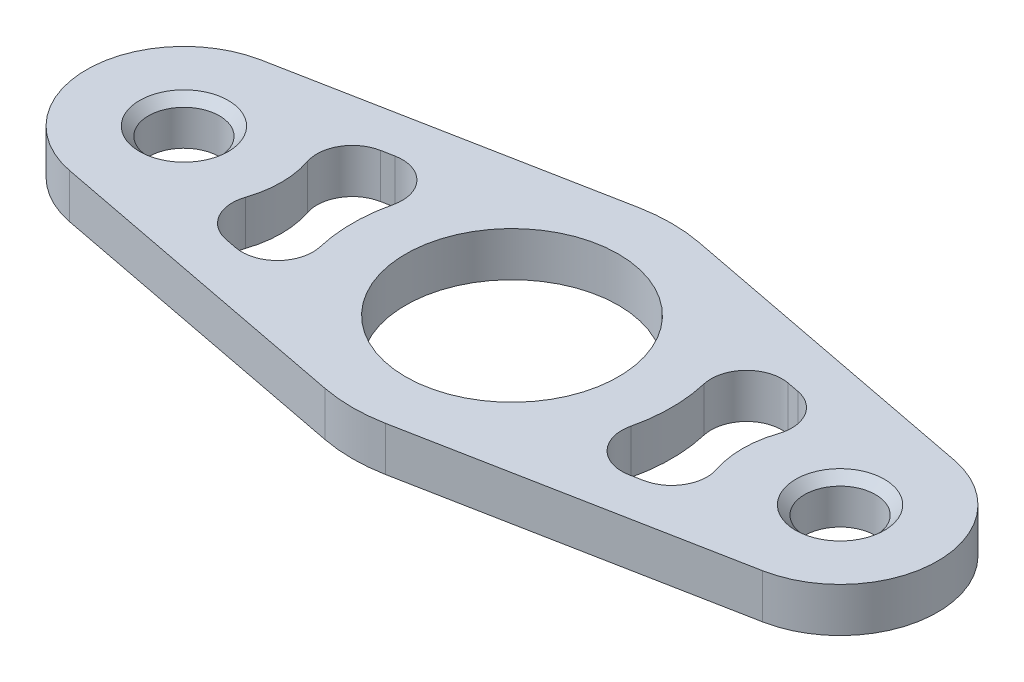
SolidWorks part; units mm, degrees
ref_plane "Front Plane" through (0, 0, 0) normal (0, 0, 1) x (1, 0, 0)
ref_plane "Top Plane" through (0, 0, 0) normal (0, 1, 0) x (1, 0, 0)
ref_plane "Right Plane" through (0, 0, 0) normal (1, 0, 0) x (0, 0, -1)
sketch "Sketch1" plane through (0, 0, 0) normal (0, 1, 0) x (1, 0, 0)
  line L0 (0, 0) -> (0, 32.3724) construction
  line L1 (37, 0) -> (-37, 0) construction
  line L2 (-39.0811, 10.8013) -> (-3.4054, 17.6749)
  line L3 (-29.0821, 7.6359) -> (-14.6845, 10.4098)
  line L4 (-29.0821, -7.6359) -> (-14.6845, -10.4098)
  line L5 (-39.0811, -10.8013) -> (-3.4054, -17.6749)
  line L6 (-38.1351, 5.8916) -> (-2.4595, 12.7652) construction
  line L7 (39.0811, -10.8013) -> (3.4054, -17.6749)
  line L8 (29.0821, -7.6359) -> (14.6845, -10.4098)
  line L9 (29.0821, 7.6359) -> (14.6845, 10.4098)
  line L10 (39.0811, 10.8013) -> (3.4054, 17.6749)
  circle A0 centre (0, 0) radius 12
  arc A1 (-14.6845, 10.4098) -> (-14.6845, -10.4098) centre (0, 0) ccw
  circle A2 centre (-37, 0) radius 4
  arc A3 (-39.0811, 10.8013) -> (-39.0811, -10.8013) centre (-37, 0) ccw
  arc A4 (-29.0821, -7.6359) -> (-29.0821, 7.6359) centre (-37, 0) ccw
  arc A5 (-3.4054, -17.6749) -> (3.4054, -17.6749) centre (0, 0) ccw
  arc A6 (29.0821, -7.6359) -> (29.0821, 7.6359) centre (37, 0) cw
  arc A7 (39.0811, 10.8013) -> (39.0811, -10.8013) centre (37, 0) cw
  circle A8 centre (37, 0) radius 4
  arc A9 (14.6845, 10.4098) -> (14.6845, -10.4098) centre (0, 0) cw
  arc A10 (3.4054, 17.6749) -> (-3.4054, 17.6749) centre (0, 0) ccw
  arc A11 (14.6845, -10.4098) -> (14.6845, 10.4098) centre (0, 0) ccw
  dimension "D1" = 36
  dimension "D2" = 24
  dimension "D3" = 22
  dimension "D4" = 8
  dimension "D5" = 37
  dimension "D7" = 5
  dimension "D6" = 5
extrude "Boss-Extrude1" add sketch "Sketch1" along normal mid plane 5 contours L10 A10 L2 A3 L5 A5 L7 A7 A8 A2 A0 L4 A4 L3 A1 A9 L9 A6 L8
fillet "Fillet1" radius 4 8 edges at (14.6845, 0, 10.4098) (29.0821, 0, 7.6359) (29.0821, 0, -7.6359) (14.6845, 0, -10.4098) (-14.6845, 0, 10.4098) (-14.6845, 0, -10.4098) (-29.0821, 0, 7.6359) (-29.0821, 0, -7.6359)
chamfer "Chamfer1" distance 1 angle 45 2 edges at (37, 2.5, 4) (-37, 2.5, 4)
